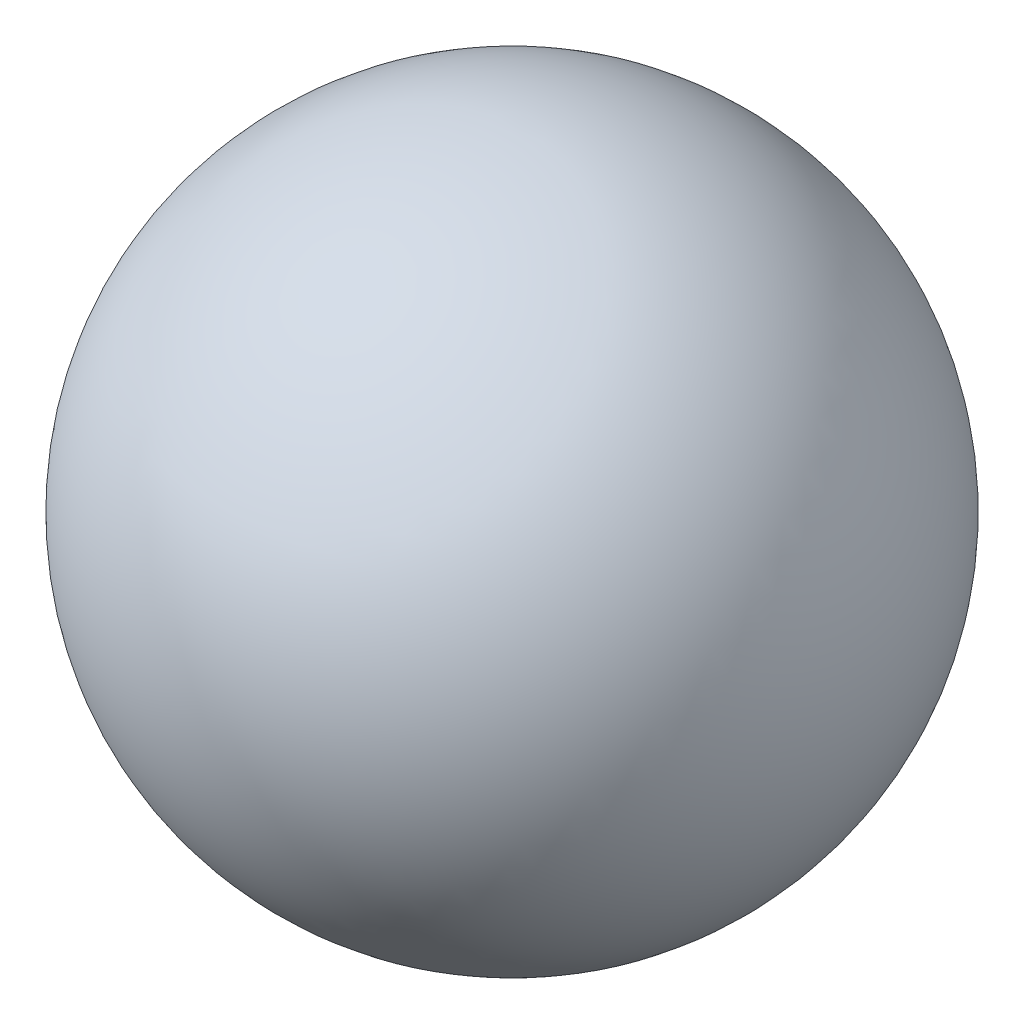
SolidWorks part; units mm, degrees
ref_plane "正面" through (0, 0, 0) normal (0, 0, 1) x (1, 0, 0)
ref_plane "平面" through (0, 0, 0) normal (0, 1, 0) x (1, 0, 0)
ref_plane "右側面" through (0, 0, 0) normal (1, 0, 0) x (0, 0, -1)
sketch "ｽｹｯﾁ1" plane through (0, 0, 0) normal (0, 0, 1) x (1, 0, 0)
  line L1 (0, 0.0489) -> (0, -0.0489)
  arc A2 (0, 0.0489) -> (0, -0.0489) centre (0, 0) cw
  point P8 (0, 0)
  dimension "D1" = 0.0489
revolve "回転2" add sketch "ｽｹｯﾁ1" angle 360 about L1
